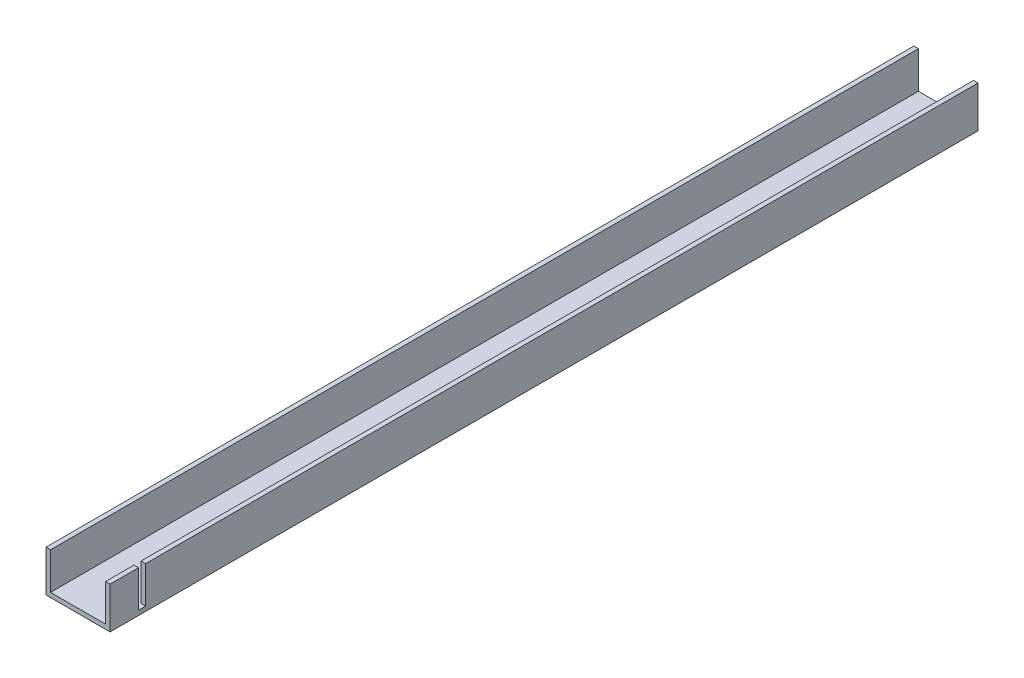
SolidWorks part; units mm, degrees
ref_plane "Front Plane" through (0, 0, 0) normal (0, 0, 1) x (1, 0, 0)
ref_plane "Top Plane" through (0, 0, 0) normal (0, 1, 0) x (1, 0, 0)
ref_plane "Right Plane" through (0, 0, 0) normal (1, 0, 0) x (0, 0, -1)
sketch "Sketch1" plane through (0, 0, 0) normal (0, 0, 1) x (1, 0, 0)
  line L0 (0, 0) -> (0, 14.55)
  line L1 (0, 14.55) -> (1.5875, 14.55)
  line L2 (1.5875, 14.55) -> (1.5875, 1.5875)
  line L3 (1.5875, 1.5875) -> (20.9125, 1.5875)
  line L4 (20.9125, 1.5875) -> (20.9125, 14.55)
  line L5 (20.9125, 14.55) -> (22.5, 14.55)
  line L6 (22.5, 14.55) -> (22.5, 0)
  line L7 (22.5, 0) -> (0, 0)
  point P3 (0, 80.1448)
  point P10 (571.5, 0)
  point P11 (5.4213, 78.2093)
  dimension "D1" = 22.5
  dimension "D2" = 14.55
  dimension "D3" = 1.5875
  dimension "D4" = 1.5875
extrude "Boss-Extrude1" add sketch "Sketch1" along normal blind 304.8 contours L0 L1 L2 L3 L4 L5 L6 L7
sketch "Sketch3" plane through (20.9125, 0, 0) normal (-1, 0, 0) x (0, 0, 1)
  line L0 (304.8, 14.55) -> (0, 14.55) construction
  line L1 (292.3, 14.55) -> (294.8, 14.55)
  line L2 (292.3, 14.55) -> (292.3, 1.5875)
  line L3 (292.3, 1.5875) -> (294.8, 1.5875)
  line L4 (294.8, 14.55) -> (294.8, 1.5875)
  line L5 (304.8, 1.5875) -> (0, 1.5875) construction
  line L6 (304.8, 1.5875) -> (304.8, 14.55) construction
  dimension "D1" = 2.5
  dimension "D2" = 10
extrude "Cut-Extrude1" cut sketch "Sketch3" against normal through all contours L2 L3 L4 L1
sketch "Sketch4" plane through (0, 1.5875, 0) normal (0, 1, 0) x (1, 0, 0)
  line L0 (1.5875, 0) -> (20.9125, 0) construction
  line L1 (10, 0) -> (12.5, 0)
  line L2 (10, 0) -> (10, -50)
  line L3 (10, -50) -> (12.5, -50)
  line L4 (12.5, 0) -> (12.5, -50)
  line L5 (1.5875, 0) -> (11.25, 0) construction
  line L6 (11.25, 0) -> (20.9125, 0) construction
  dimension "D1" = 2.5
  dimension "D2" = 50
extrude "Cut-Extrude2" cut sketch "Sketch4" against normal through all contours L2 L3 L4 L1
